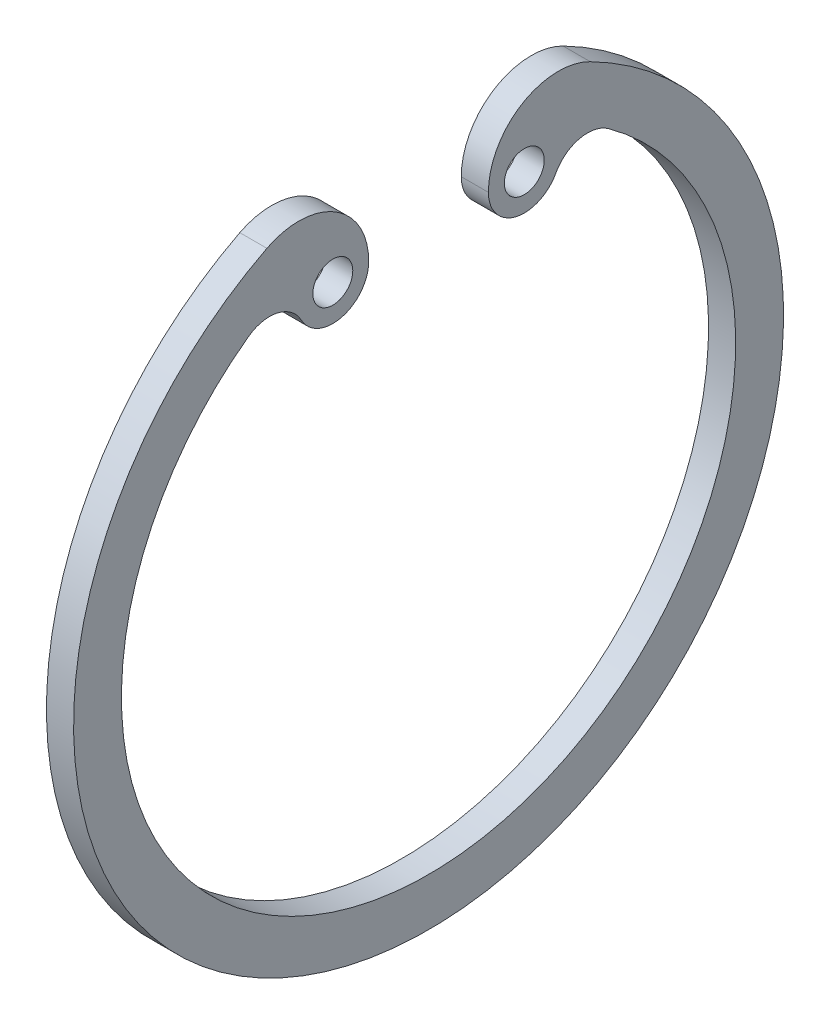
SolidWorks part; units mm, degrees
material "AISI Тип A2 Инструментальная сталь"
ref_plane "Спереди" through (0, 0, 0) normal (0, 0, 1) x (1, 0, 0)
ref_plane "Сверху" through (0, 0, 0) normal (0, 1, 0) x (1, 0, 0)
ref_plane "Справа" through (0, 0, 0) normal (1, 0, 0) x (0, 0, -1)
sketch "Эскиз1" plane through (0, 0, 0) normal (1, 0, 0) x (0, 0, -1)
  line L0 (0, -1000) -> (0, 49000) construction
  arc A0 (-10.1311, 19.8097) -> (10.1311, 19.8097) centre (0, 0) ccw
  arc A1 (-11.2818, 15.5975) -> (11.2818, 15.5975) centre (0, 0) ccw
  circle A2 centre (-6, 15.906) radius 1.25
  arc A3 (-7.9816, 14.8402) -> (-3.75, 15.906) centre (-6, 15.906) ccw
  arc A4 (-10.1311, 19.8097) -> (-3.75, 15.906) centre (-8.1346, 15.906) cw
  arc A5 (-11.2818, 15.5975) -> (-7.9816, 14.8402) centre (-9.9632, 13.7745) cw
  circle A6 centre (6, 15.906) radius 1.25
  arc A7 (11.2818, 15.5975) -> (7.9816, 14.8402) centre (9.9632, 13.7745) ccw
  arc A8 (7.9816, 14.8402) -> (3.75, 15.906) centre (6, 15.906) cw
  arc A9 (10.1311, 19.8097) -> (3.75, 15.906) centre (8.1346, 15.906) ccw
  dimension "D1" = 44.5
  dimension "D2" = 3
  dimension "D3" = 2.5
  dimension "D4" = 1
  dimension "D5" = 6
extrude "Бобышка-Вытянуть1" add sketch "Эскиз1" along normal blind 1.7
